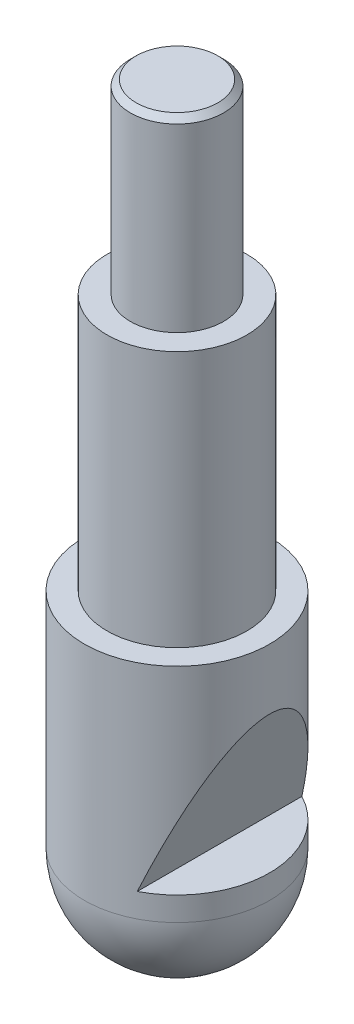
SolidWorks part; units mm, degrees
ref_plane "Plan1" through (0, 0, 0) normal (0, 0, 1) x (1, 0, 0)
ref_plane "Plan2" through (0, 0, 0) normal (0, 1, 0) x (1, 0, 0)
ref_plane "Plan3" through (0, 0, 0) normal (1, 0, 0) x (0, 0, -1)
sketch "Esquisse1" plane through (0, 0, 0) normal (0, 0, 1) x (1, 0, 0)
  line L1 (0, 65) -> (4, 65)
  line L2 (4, 65) -> (4, 49)
  line L3 (4, 49) -> (6, 49)
  line L4 (6, 49) -> (6, 27)
  line L5 (6, 27) -> (7.95, 27)
  line L6 (7.95, 27) -> (7.95, 7.95)
  line L7 (0, -9.2814) -> (0, 77.9025) construction
  line L8 (0, 65) -> (0, 0)
  arc A0 (0, 0) -> (7.95, 7.95) centre (0, 7.95) ccw
  dimension "D5" = 22
  dimension "D8" = 7.95
  dimension "D1" = 4
  dimension "D2" = 4
  dimension "D3" = 6
  dimension "D4" = 16
  dimension "D6" = 27
  dimension "D7" = 7.95
revolve "Base-Révolution" add sketch "Esquisse1"
cosmetic thread "Représentation de filetage1"
chamfer "Chanfrein1" distance 0.5 angle 45
sketch "Esquisse2" plane through (0, 0, 0) normal (0, 0, 1) x (1, 0, 0)
  line L0 (14.6175, 1) -> (14.6175, 10)
  line L1 (23.9468, -11.0839) -> (-11.5324, -11.0839)
  line L2 (3.65, 10) -> (7.95, 21.8)
  line L3 (14.6175, 1) -> (-11.5324, 1)
  line L4 (-11.5324, -11.0839) -> (-11.5324, 1)
  line L5 (14.6175, 10) -> (3.65, 10)
  line L6 (7.95, 7.95) -> (7.95, 27) construction
  line L7 (7.95, 21.8) -> (23.9468, 21.8)
  line L8 (23.9468, 21.8) -> (23.9468, -11.0839)
  line L9 (-7.95, 27) -> (-7.95, 7.95) construction
  dimension "D1" = 1
  dimension "D2" = 9
  dimension "D3" = 11.6
  dimension "D4" = 11.5324
  dimension "D5" = 11.8
extrude "Enlèv. mat.-Extru.1" cut sketch "Esquisse2" against normal through all and the other way through all
